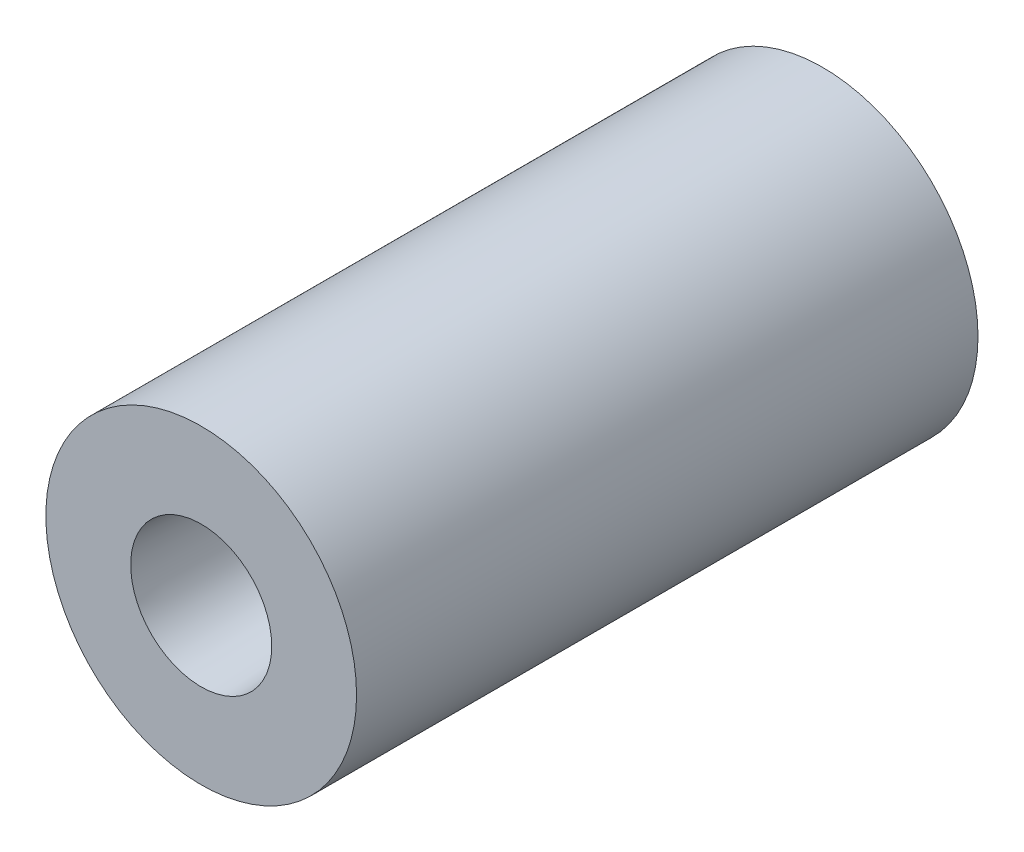
SolidWorks part; units mm, degrees
ref_plane "Front Plane" through (0, 0, 0) normal (0, 0, 1) x (1, 0, 0)
ref_plane "Top Plane" through (0, 0, 0) normal (0, 1, 0) x (1, 0, 0)
ref_plane "Right Plane" through (0, 0, 0) normal (1, 0, 0) x (0, 0, -1)
sketch "Sketch1" plane through (0, 0, 0) normal (0, 0, 1) x (1, 0, 0)
  circle A0 centre (0, 0) radius 5
  dimension "D1" = 10
extrude "Boss-Extrude1" add sketch "Sketch1" along normal blind 20
sketch "Sketch2" plane through (0, 0, 0) normal (0, 0, 1) x (1, 0, 0)
  circle A0 centre (0, 0) radius 2.27
  dimension "D1" = 4.54
extrude "Cut-Extrude1" cut sketch "Sketch2" along a picked direction on the side of the normal blind 5.68 draft 3.074
sketch "Sketch7" plane through (0, 0, 0) normal (0, 0, 1) x (1, 0, 0)
  circle A0 centre (0, 0) radius 1
extrude "Cut-Extrude2" cut sketch "Sketch7" along normal through all
sketch "Sketch9" plane through (0, 0, 20) normal (0, 0, 1) x (1, 0, 0)
  circle A0 centre (0, 0) radius 2.27
  circle A1 centre (0, 0) radius 2.27 construction
extrude "Cut-Extrude3" cut sketch "Sketch9" against normal blind 5.68 draft 3.074
